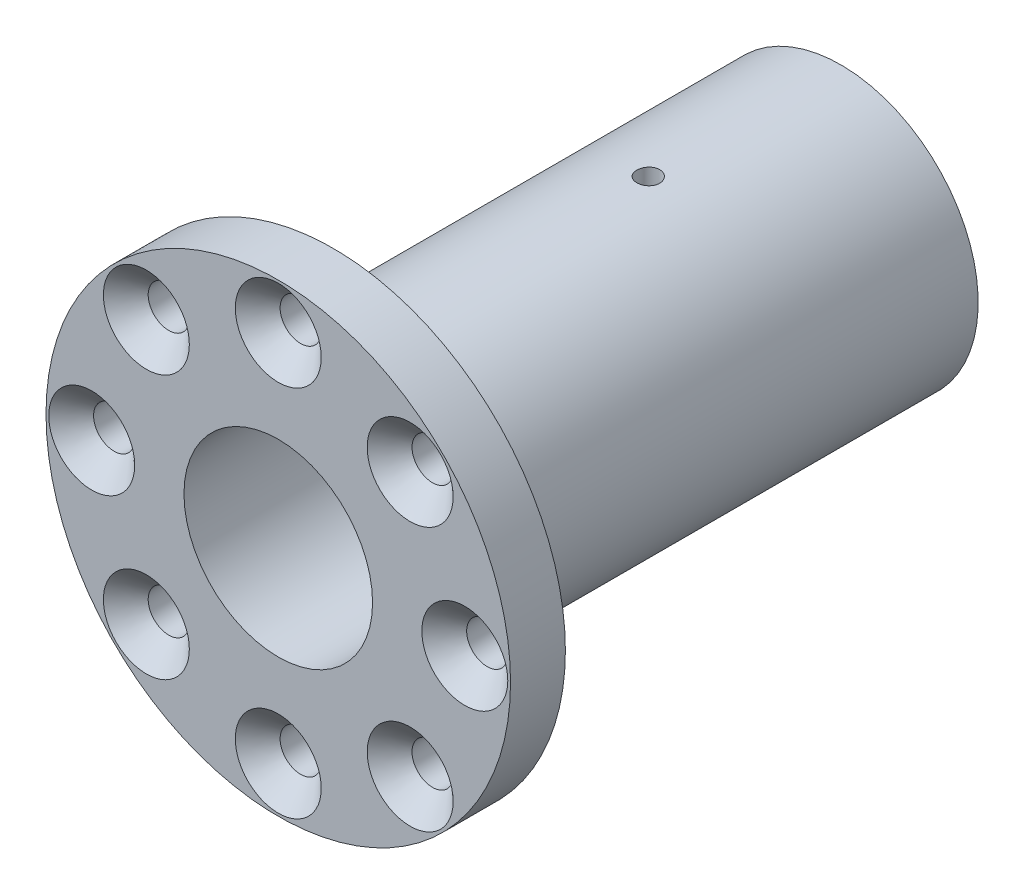
SolidWorks part; units mm, degrees
ref_plane "Front Plane" through (0, 0, 0) normal (0, 0, 1) x (1, 0, 0)
ref_plane "Top Plane" through (0, 0, 0) normal (0, 1, 0) x (1, 0, 0)
ref_plane "Right Plane" through (0, 0, 0) normal (1, 0, 0) x (0, 0, -1)
ref_plane "Plane1" through (0, 0, 0) normal (0, -1, 0) x (1, 0, 0)
sketch "Sketch1" plane through (0, 0, 0) normal (0, -1, 0) x (1, 0, 0)
  line L0 (25.4, 61.54) -> (0, 61.54)
  line L1 (0, 61.54) -> (0, 55.54)
  line L2 (0, 55.54) -> (25.4, 55.54)
  line L3 (25.4, 55.54) -> (25.4, 61.54)
  line L4 (0, 61.54) -> (0, 55.54) construction
revolve "Revolve1" add sketch "Sketch1" angle 360 about L4
sketch "Sketch2" plane through (0, 0, 55.54) normal (0, 0, -1) x (-1, 0, 0)
  circle A0 centre (0, 0) radius 15
extrude "Boss-Extrude1" add sketch "Sketch2" along normal blind 55.54
sketch "Sketch3" plane through (0, 0, 0) normal (0, 0, -1) x (-1, 0, 0)
  line L0 (2.5, 9.0585) -> (-2.5, 9.0585)
  line L1 (-2.5, 9.0585) -> (-2.5, 6.5383)
  line L2 (2.5, 6.5383) -> (2.5, 9.0585)
  arc A0 (-2.5, 6.5383) -> (2.5, 6.5383) centre (0, 0) cw
extrude "Cut-Extrude1" cut sketch "Sketch3" against normal through all
sketch "Sketch4" plane through (0, 0, 0) normal (0, -1, 0) x (1, 0, 0)
  line L0 (7.0104, 61.54) -> (0, 61.54)
  line L1 (0, 61.54) -> (0, 0)
  line L2 (0, 0) -> (7.0104, 0)
  line L3 (7.0104, 0) -> (7.0104, 61.54)
  line L4 (0, 61.54) -> (0, 0) construction
  dimension "D1" = 7.0104
revolve "Cut-Revolve1" cut sketch "Sketch4" angle 360 about L4
hole_wizard "#2 Clearance Hole1" positions "Sketch6" profile "Sketch5" hole size "#2" standard "ANSI Inch"
sketch "Sketch6" plane through (0, 0, 0) normal (0, 0, -1) x (-1, 0, 0)
  point P0 (-11.5, 0)
  point P1 (-5.75, -9.9593)
  point P2 (5.75, -9.9593)
  point P3 (11.5, 0)
  point P4 (5.75, 9.9593)
  point P5 (-5.75, 9.9593)
sketch "Sketch5" plane through (11.5, 0, 0) normal (1, 0, 0) x (0, 1, 0)
  line L0 (0, 0) -> (0, 12)
  line L1 (0, 12) -> (1.25, 12)
  line L2 (1.25, 12) -> (1.25, 0)
  line L5 (1.25, 0) -> (0, 0)
  line L10 (0, 12) -> (-1.25, 12) construction
  line L11 (0, -6.35) -> (0, 107.95) construction
  dimension "Hole Dia." = 2.5
  dimension "Hole Depth" = 12
  dimension "Drill Angle" = 180
hole_wizard "#2 Clearance Hole2" positions "Sketch8" profile "Sketch7" hole size "#2" standard "ANSI Inch"
sketch "Sketch8" plane through (0, 9.0585, 0) normal (0, -1, 0) x (-1, 0, 0)
  line L0 (15, 0) -> (-15, 0) construction
  point P0 (0, -21.082)
  dimension "D1" = 21.082
sketch "Sketch7" plane through (0, 9.0585, 21.082) normal (1, 0, 0) x (0, 0, -1)
  line L0 (0, 0) -> (0, 16.3415)
  line L1 (0, 16.3415) -> (1.25, 16.3415)
  line L2 (1.25, 16.3415) -> (1.25, 0)
  line L5 (1.25, 0) -> (0, 0)
  line L11 (0, -6.35) -> (0, 107.95) construction
  dimension "Thru Hole Dia." = 2.5
  dimension "Thru Hole Depth" = 16.3415
hole_wizard "CSK for #8 Flat Head Machine Screw (100)1" positions "Sketch10" profile "Sketch9" countersink size "#8" standard "ANSI Inch"
sketch "Sketch10" plane through (0, 0, 61.54) normal (0, 0, 1) x (1, 0, 0)
  point P0 (0, 20.4)
  point P1 (14.425, 14.425)
  point P2 (20.4, 0)
  point P3 (14.425, -14.425)
  point P4 (0, -20.4)
  point P5 (-14.425, -14.425)
  point P6 (-20.4, 0)
  point P7 (-14.425, 14.425)
sketch "Sketch9" plane through (0, 20.4, 61.54) normal (1, 0, 0) x (0, -1, 0)
  line L0 (0, 0) -> (0, 61.54)
  line L1 (0, 61.54) -> (2.25, 61.54)
  line L2 (2.25, 61.54) -> (2.25, 2.45)
  line L3 (2.25, 2.45) -> (4.7, 0)
  line L5 (4.7, 0) -> (0, 0)
  line L6 (-2.25, 2.45) -> (-4.7, 0) construction
  line L11 (0, -6.35) -> (0, 107.95) construction
  dimension "Thru Hole Dia." = 4.5
  dimension "Thru Hole Depth" = 61.54
  dimension "Near C'Sink Dia." = 9.4
  dimension "Near C'Sink Angle" = 90
sketch "Sketch11" plane through (0, 0, 61.54) normal (0, 0, 1) x (1, 0, 0)
  circle A0 centre (0, 0) radius 10.3124
  dimension "D1" = 20.6248
extrude "Cut-Extrude2" cut sketch "Sketch11" against normal blind 38.1
